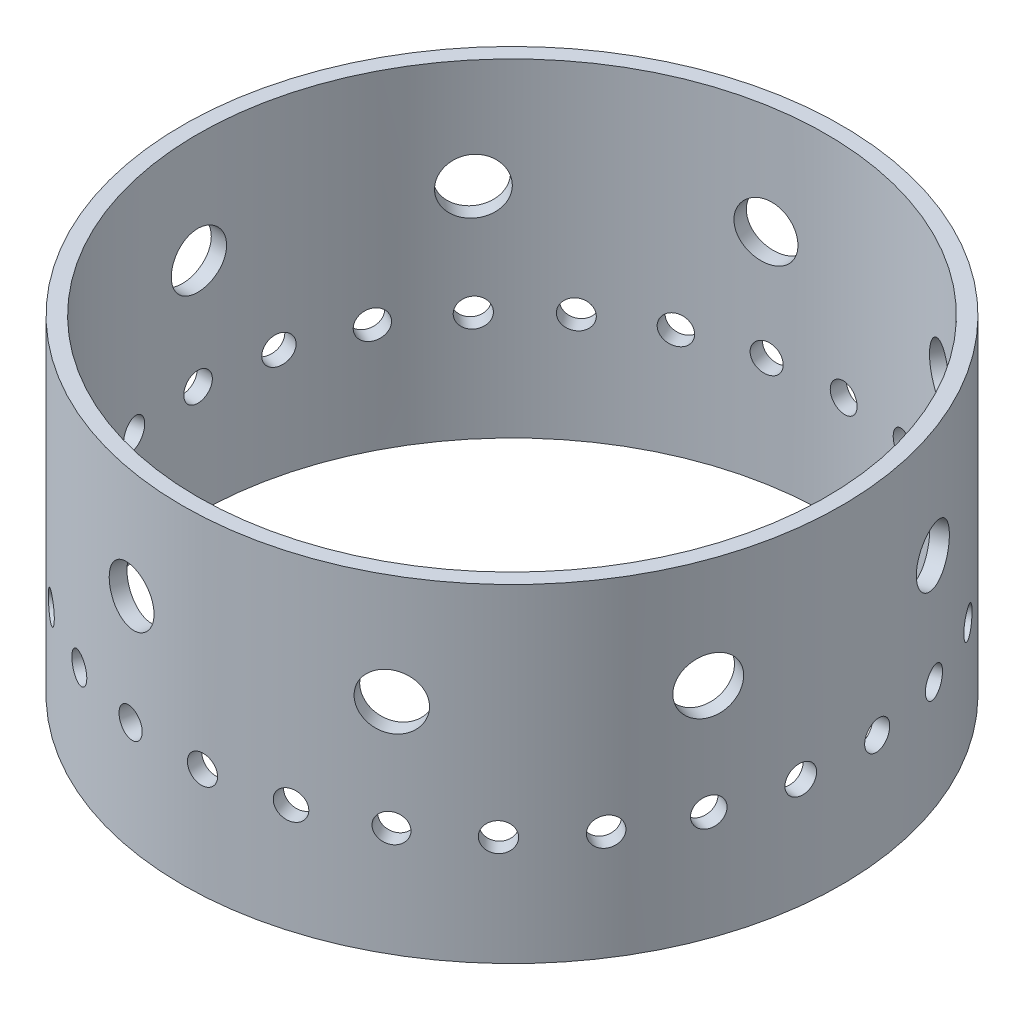
SolidWorks part; units mm, degrees
ref_plane "Front Plane" through (0, 0, 0) normal (0, 0, 1) x (1, 0, 0)
ref_plane "Top Plane" through (0, 0, 0) normal (0, 1, 0) x (1, 0, 0)
ref_plane "Right Plane" through (0, 0, 0) normal (1, 0, 0) x (0, 0, -1)
sketch "Sketch1" plane through (0, 0, 0) normal (0, 1, 0) x (1, 0, 0)
  circle A0 centre (0, 0) radius 65.405
  circle A1 centre (0, 0) radius 68.58
  dimension "D1" = 130.81
  dimension "D2" = 137.16
extrude "Boss-Extrude1" add sketch "Sketch1" along normal blind 68.326
sketch "Sketch2" plane through (0, 0, 0) normal (1, 0, 0) x (0, 0, -1)
  line L0 (0, 0) -> (0, 82.5802) construction
sketch "Sketch3" plane through (0, 0, 0) normal (1, 0, 0) x (0, 0, -1)
  line L0 (0, 0) -> (0, 82.5802) construction
  line L1 (-68.58, 0) -> (68.58, 0) construction
  circle A0 centre (0, 22.7753) radius 2.9718
  dimension "D1" = 5.9436
  dimension "D2" = 22.7753
extrude "Cut-Extrude1" cut sketch "Sketch3" against normal blind 80.01
pattern_circular "CirPattern1" count 27 over 360 about axis through (0, 0, 0) along (0, 1, 0) of "Cut-Extrude1"
sketch "Sketch4" plane through (0, 0, 0) normal (1, 0, 0) x (0, 0, -1)
  line L0 (0, 0) -> (0, 82.5802) construction
  line L1 (68.58, 68.326) -> (-68.58, 68.326) construction
  circle A0 centre (0, 45.5507) radius 5.7506
  dimension "D1" = 11.5011
  dimension "D2" = 22.7753
extrude "Cut-Extrude2" cut sketch "Sketch4" against normal blind 80.01
pattern_circular "CirPattern2" count 9 over 360 about axis through (0, 0, 0) along (0, 1, 0) of "Cut-Extrude2"
